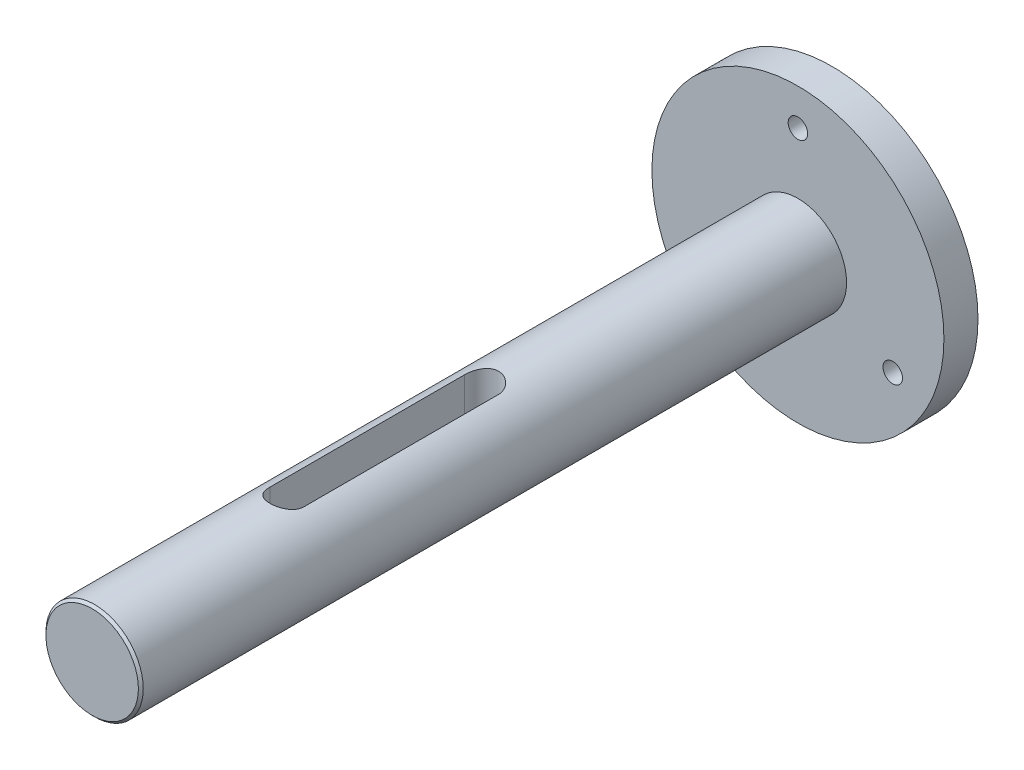
SolidWorks part; units mm, degrees
ref_plane "Front Plane" through (0, 0, 0) normal (0, 0, 1) x (1, 0, 0)
ref_plane "Top Plane" through (0, 0, 0) normal (0, 1, 0) x (1, 0, 0)
ref_plane "Right Plane" through (0, 0, 0) normal (1, 0, 0) x (0, 0, -1)
sketch "Sketch1" plane through (0, 0, 0) normal (0, 0, 1) x (1, 0, 0)
  line L0 (0, 0) -> (0, 22.5) construction
  circle A0 centre (0, 0) radius 30
  circle A1 centre (0, 22.5) radius 2
  circle A2 centre (19.4856, -11.25) radius 2
  circle A3 centre (-19.4856, -11.25) radius 2
  circle A4 centre (0, 0) radius 22.5 construction
  point P11 (0, 0)
  dimension "D1" = 60
  dimension "D3" = 4
  dimension "D4" = 45
  dimension "D2" = 3
extrude "Boss-Extrude1" add sketch "Sketch1" along normal blind 7
sketch "Sketch2" plane through (0, 0, 7) normal (0, 0, 1) x (1, 0, 0)
  circle A0 centre (0, 0) radius 10
  dimension "D1" = 20
extrude "Boss-Extrude2" add sketch "Sketch2" along normal blind 145
sketch "Sketch3" plane through (0, 0, 0) normal (0, 1, 0) x (1, 0, 0)
  line L0 (0, 0) -> (0, -152) construction
  line L1 (-10, -152) -> (10, -152) construction
  line L2 (0, -72) -> (0, -112) construction
  line L3 (3.5, -72) -> (3.5, -112)
  line L4 (-3.5, -72) -> (-3.5, -112)
  arc A0 (3.5, -72) -> (-3.5, -72) centre (0, -72) ccw
  arc A1 (-3.5, -112) -> (3.5, -112) centre (0, -112) ccw
  point P7 (0, -92)
  dimension "D1" = 40
  dimension "D2" = 65
  dimension "D3" = 7
extrude "Cut-Extrude1" cut sketch "Sketch3" along normal blind 25 and the other way blind 1.5
chamfer "Chamfer2" distance 1.5 angle 45 4 edges at (0, -1.5, 115.5) (3.5, -1.5, 92) (-3.5, -1.5, 92) (0, -1.5, 68.5)
sketch "Sketch4" plane through (0, 0, 0) normal (0, 1, 0) x (1, 0, 0)
  line L0 (0, -72) -> (0, -112) construction
  line L1 (2, -72) -> (2, -112)
  line L2 (-2, -72) -> (-2, -112)
  line L3 (0, -70) -> (1.4896, -70) construction
  line L4 (0, -114) -> (2.8723, -114) construction
  arc A0 (2, -72) -> (-2, -72) centre (0, -72) ccw
  arc A1 (-2, -112) -> (2, -112) centre (0, -112) ccw
  arc A3 (2, -72) -> (-2, -72) centre (0, -72) ccw construction
  arc A4 (-2, -112) -> (2, -112) centre (0, -112) ccw construction
  arc A6 (-3.5, -112) -> (3.5, -112) centre (0, -112) ccw construction
  point P3 (0, -92)
  dimension "D1" = 4
extrude "Cut-Extrude2" cut sketch "Sketch4" against normal blind 25
chamfer "Chamfer1" distance 0.5 angle 45 1 edges at (10, 0, 152)
